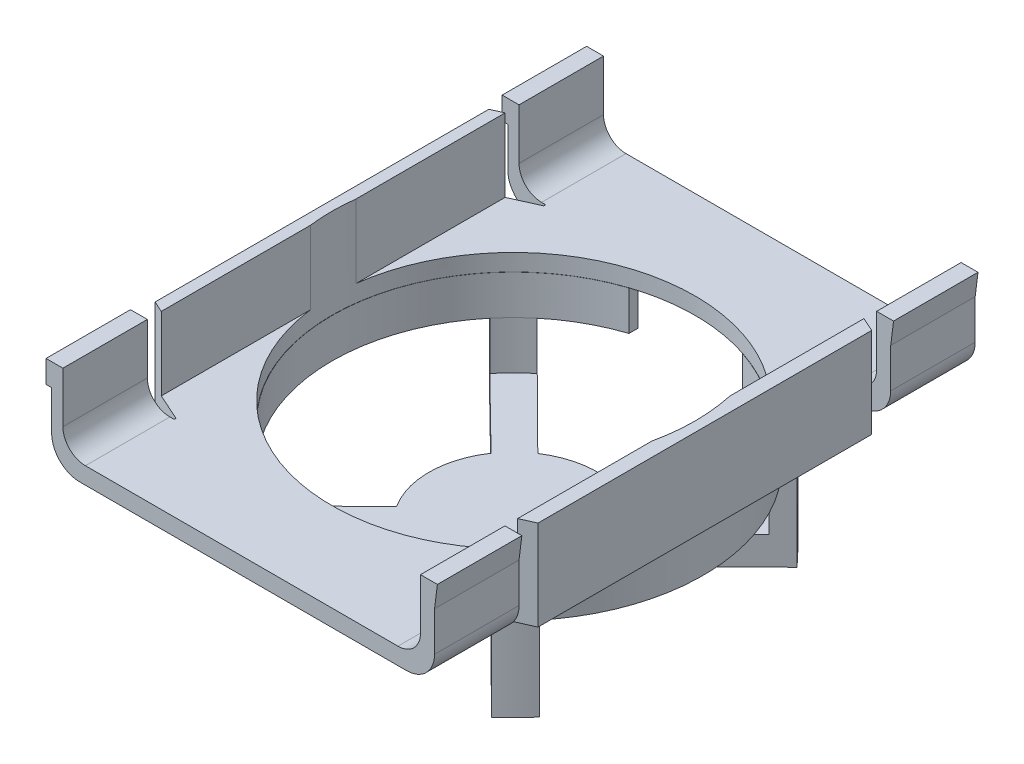
SolidWorks part; units mm, degrees
material "ABS"
ref_plane "Front Plane" through (0, 0, 0) normal (0, 0, 1) x (1, 0, 0)
ref_plane "Top Plane" through (0, 0, 0) normal (0, 1, 0) x (1, 0, 0)
ref_plane "Right Plane" through (0, 0, 0) normal (1, 0, 0) x (0, 0, -1)
sketch "Sketch1" plane through (0, 0, 0) normal (0, 0, 1) x (1, 0, 0)
  line L0 (-35.5691, 10.2526) -> (-35.5691, 6.2526)
  line L1 (-29.5691, -5.7474) -> (28.4309, -5.7474)
  line L2 (-35.5691, 10.2526) -> (-32.5691, 10.2526)
  line L3 (-28.5691, -2.7474) -> (26.9309, -2.7474)
  line L4 (33.9309, 10.2526) -> (30.9309, 10.2526)
  line L5 (-35.5691, 6.2526) -> (-34.5691, 6.2526)
  line L6 (-34.5691, 6.2526) -> (-34.5691, -0.7474)
  line L7 (33.9309, 10.2526) -> (33.4309, 6.2526)
  line L8 (33.4309, 6.2526) -> (33.4309, -0.7474)
  line L9 (30.9309, 10.2526) -> (30.9309, 1.2526)
  line L10 (-29.5691, -5.7474) -> (-29.5691, -1.3005) construction
  line L11 (-32.5691, 10.2526) -> (-32.5691, 1.2526)
  arc A0 (33.4309, -0.7474) -> (28.4309, -5.7474) centre (28.4309, -0.7474) cw
  arc A1 (-34.5691, -0.7474) -> (-29.5691, -5.7474) centre (-29.5691, -0.7474) ccw
  arc A2 (-28.5691, -2.7474) -> (-32.5691, 1.2526) centre (-28.5691, 1.2526) cw
  arc A3 (30.9309, 1.2526) -> (26.9309, -2.7474) centre (26.9309, 1.2526) cw
  dimension "D1" = 5
  dimension "D2" = 4
  dimension "D3" = 4
extrude "Boss-Extrude1" add sketch "Sketch1" along normal blind 15
sketch "Sketch2" plane through (0, 0, 15) normal (0, 0, 1) x (1, 0, 0)
  line L1 (33.4309, -5.7474) -> (-34.5691, -5.7474)
  line L2 (-34.5691, -5.7474) -> (-34.5691, 10.2526)
  line L3 (-32.5691, 10.2526) -> (-35.5691, 10.2526) construction
  line L4 (-34.5691, 10.2526) -> (-32.5691, 10.2526)
  line L5 (-32.5691, 10.2526) -> (-32.5691, -2.7474)
  line L6 (-32.5691, -2.7474) -> (30.9309, -2.7474)
  line L7 (33.4309, -5.7474) -> (33.4309, 10.2526)
  line L10 (33.9309, 10.2526) -> (30.9309, 10.2526) construction
  line L11 (33.4309, 10.2526) -> (30.9309, 10.2526)
  line L12 (30.9309, 10.2526) -> (30.9309, -2.7474)
extrude "Boss-Extrude2" add sketch "Sketch2" along normal blind 66
ref_plane "Plane1" through (0, 0, 48) normal (0, 0, -1) x (-1, 0, 0)
mirror "Mirror1" about plane through (0, 0, 48) normal (0, 0, -1) of "Boss-Extrude1"
sketch "Sketch4" plane through (0, -5.7474, 0) normal (0, -1, 0) x (1, 0, 0)
  line L0 (-34.5691, 15) -> (-27.0691, 15)
  line L1 (-27.0691, 15) -> (-34.5691, 18.37)
  line L2 (-34.5691, 81) -> (-34.5691, 15) construction
  line L3 (-34.5691, 18.37) -> (-34.5691, 15)
  line L4 (-29.5691, 96) -> (28.4309, 96) construction
  line L7 (-0.5691, 96) -> (-0.5691, 0) construction
  line L8 (-29.5691, 0) -> (28.4309, 0) construction
  line L9 (-0.5691, 48) -> (-34.5691, 48) construction
  line L10 (33.4309, 18.37) -> (33.4309, 15)
  line L11 (25.9309, 15) -> (33.4309, 18.37)
  line L12 (33.4309, 15) -> (25.9309, 15)
  line L13 (33.4309, 81) -> (25.9309, 81)
  line L14 (25.9309, 81) -> (33.4309, 77.63)
  line L15 (33.4309, 77.63) -> (33.4309, 81)
  line L16 (-34.5691, 77.63) -> (-34.5691, 81)
  line L17 (-27.0691, 81) -> (-34.5691, 77.63)
  line L18 (-34.5691, 81) -> (-27.0691, 81)
  dimension "D1" = 3.37
  dimension "D2" = 7.5
extrude "Cut-Extrude1" cut sketch "Sketch4" against normal up to surface (16 mm away) up to face at (33.0559, 10.2526, 48)
fillet "Fillet1" radius 0.2 4 edges at (-27.0691, -4.2474, 81) (-27.0691, -4.2474, 15) (25.9309, -4.2474, 81) (25.9309, -4.2474, 15)
sketch "Sketch5" plane through (0, -5.7474, 0) normal (0, -1, 0) x (1, 0, 0)
  line L0 (-29.5691, 96) -> (28.4309, 96) construction
  line L3 (-0.5691, 96) -> (-0.5691, 0) construction
  line L4 (-29.5691, 0) -> (28.4309, 0) construction
  line L5 (-0.5691, 48) -> (-34.5691, 48) construction
  line L6 (-34.5691, 77.63) -> (-34.5691, 18.37) construction
  circle A0 centre (-0.5691, 48) radius 32.25
  dimension "D1" = 64.5
extrude "Cut-Extrude2" cut sketch "Sketch5" against normal blind 66
ref_plane "Plane2" through (0, -26.2474, 0) normal (0, 1, 0) x (1, 0, 0)
sketch "Sketch14" plane through (0, -5.7474, 0) normal (0, -1, 0) x (1, 0, 0)
  line L2 (-10.6477, 80.1756) -> (-10.6477, 78.6001)
  line L3 (9.5094, 17.3999) -> (9.5094, 15.8244)
  line L4 (9.5094, 80.1756) -> (9.5094, 78.6001)
  line L6 (-10.6477, 17.3999) -> (-10.6477, 15.8244)
  arc A0 (-10.6477, 78.6001) -> (-10.6477, 17.3999) centre (-0.5691, 48) ccw
  arc A1 (-10.6477, 80.1756) -> (-10.6477, 15.8244) centre (-0.5691, 48) ccw
  arc A2 (9.5094, 17.3999) -> (9.5094, 78.6001) centre (-0.5691, 48) ccw
  arc A3 (9.5094, 15.8244) -> (9.5094, 80.1756) centre (-0.5691, 48) ccw
  dimension "D1" = 64.4343
  dimension "D2" = 1.5
extrude "Boss-Extrude7" add sketch "Sketch14" along normal blind 7
sketch "Sketch15" plane through (0, -12.7474, 0) normal (0, -1, 0) x (1, 0, 0)
  line L3 (-28.0261, 70.8436) -> (-25.5303, 68.3676)
  line L4 (22.6605, 75.1312) -> (20.1677, 72.6552)
  line L5 (-23.7988, 75.1312) -> (-21.306, 72.6552)
  line L6 (26.8878, 70.8436) -> (24.392, 68.3676)
  line L7 (19.9968, 23.2021) -> (22.4927, 20.726)
  line L9 (-21.1351, 23.2021) -> (-23.6309, 20.726)
  line L21 (-25.3511, 27.4148) -> (-27.857, 24.9547)
  line L23 (24.2129, 27.4148) -> (26.7188, 24.9547)
  arc A0 (-25.3511, 27.4148) -> (-21.1351, 23.2021) centre (-0.5691, 48) ccw
  arc A1 (-23.7988, 75.1312) -> (-28.0261, 70.8436) centre (-0.5691, 48) ccw
  arc A2 (26.8878, 70.8436) -> (22.6605, 75.1312) centre (-0.5691, 48) ccw
  arc A3 (-21.306, 72.6552) -> (-25.5303, 68.3676) centre (-0.5691, 48) ccw
  arc A4 (22.4927, 20.726) -> (26.7188, 24.9547) centre (-0.5691, 48) ccw
  arc A5 (24.392, 68.3676) -> (20.1677, 72.6552) centre (-0.5691, 48) ccw
  arc A7 (-27.857, 24.9547) -> (-23.6309, 20.726) centre (-0.5691, 48) ccw
  arc A8 (19.9968, 23.2021) -> (24.2129, 27.4148) centre (-0.5691, 48) ccw
  point P8 (-0.5691, 48)
  point P11 (-0.5691, 48)
extrude "Boss-Extrude9" add sketch "Sketch15" along normal up to surface (13.5 mm away) and the other way up to next (7 mm away) up to plane "Plane2"
sketch "Sketch17" plane through (0, -26.2474, 0) normal (0, -1, 0) x (1, 0, 0)
  line L0 (-21.1351, 23.2021) -> (-23.6309, 20.726) construction
  line L1 (-27.857, 24.9547) -> (-25.3511, 27.4148) construction
  line L2 (22.4927, 20.726) -> (19.9968, 23.2021) construction
  line L3 (24.2129, 27.4148) -> (26.7188, 24.9547) construction
  line L4 (26.8878, 70.8436) -> (24.392, 68.3676) construction
  line L5 (20.1677, 72.6552) -> (22.6605, 75.1312) construction
  line L6 (-23.7988, 75.1312) -> (-21.306, 72.6552) construction
  line L7 (-25.5303, 68.3676) -> (-28.0261, 70.8436) construction
  line L8 (-8.7874, 35.4517) -> (-23.6309, 20.726)
  line L9 (-27.857, 24.9547) -> (-12.9736, 39.5661)
  line L10 (22.4927, 20.726) -> (7.6491, 35.4517)
  line L11 (11.8353, 39.5661) -> (26.7188, 24.9547)
  line L12 (26.8878, 70.8436) -> (12.0443, 56.118)
  line L13 (7.8463, 60.417) -> (22.6605, 75.1312)
  line L14 (-23.7988, 75.1312) -> (-8.9845, 60.417)
  line L15 (-13.1826, 56.118) -> (-28.0261, 70.8436)
  arc A0 (-13.1826, 56.118) -> (-12.9736, 39.5661) centre (-0.5691, 48) ccw
  arc A1 (-27.857, 24.9547) -> (-23.6309, 20.726) centre (-0.5691, 48) ccw construction
  arc A2 (22.4927, 20.726) -> (26.7188, 24.9547) centre (-0.5691, 48) ccw construction
  arc A3 (26.8878, 70.8436) -> (22.6605, 75.1312) centre (-0.5691, 48) ccw construction
  arc A4 (-23.7988, 75.1312) -> (-28.0261, 70.8436) centre (-0.5691, 48) ccw construction
  arc A5 (-27.857, 24.9547) -> (-23.6309, 20.726) centre (-0.5691, 48) ccw
  arc A6 (22.4927, 20.726) -> (26.7188, 24.9547) centre (-0.5691, 48) ccw
  arc A7 (26.8878, 70.8436) -> (22.6605, 75.1312) centre (-0.5691, 48) ccw
  arc A8 (-23.7988, 75.1312) -> (-28.0261, 70.8436) centre (-0.5691, 48) ccw
  arc A9 (7.8463, 60.417) -> (-8.9845, 60.417) centre (-0.5691, 48) ccw
  arc A10 (11.8353, 39.5661) -> (12.0443, 56.118) centre (-0.5691, 48) ccw
  arc A11 (-8.7874, 35.4517) -> (7.6491, 35.4517) centre (-0.5691, 48) ccw
  dimension "D1" = 30
extrude "Boss-Extrude10" add sketch "Sketch17" against normal blind 5
